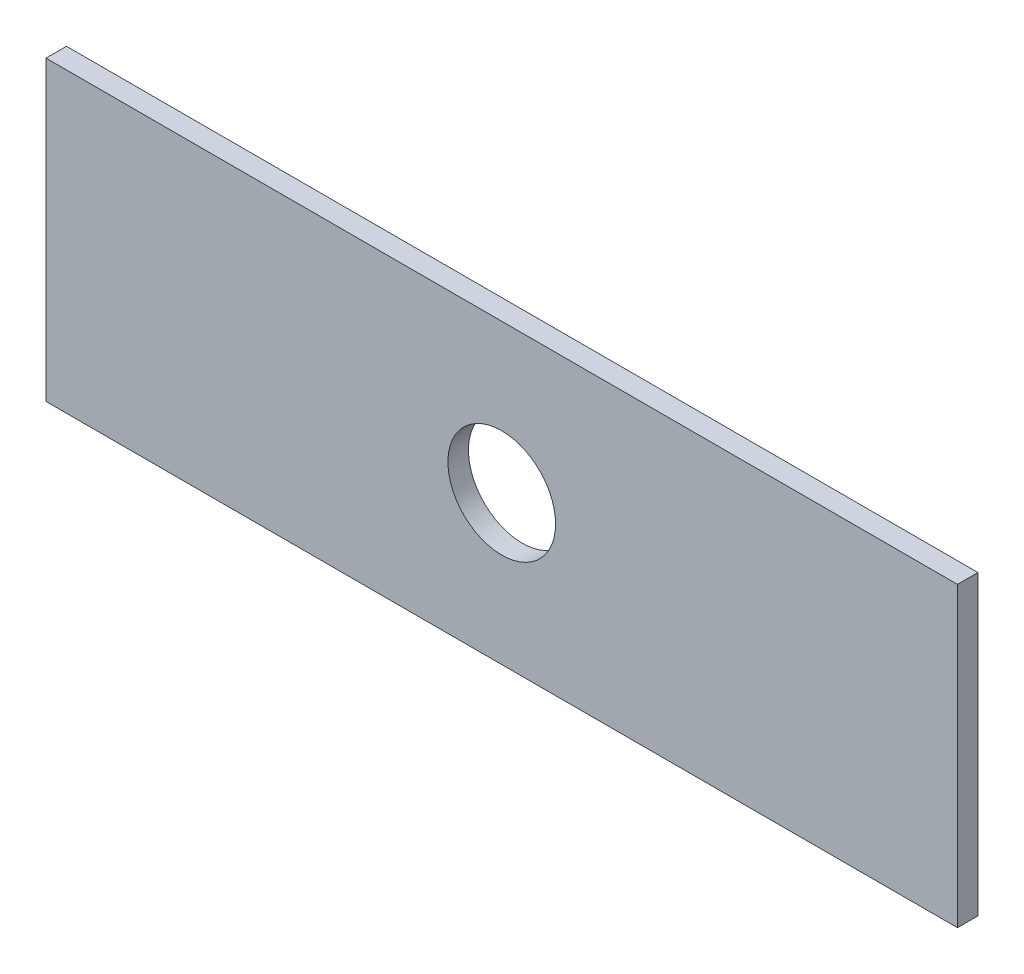
SolidWorks part; units mm, degrees
ref_plane "Front Plane" through (0, 0, 0) normal (0, 0, 1) x (1, 0, 0)
ref_plane "Top Plane" through (0, 0, 0) normal (0, 1, 0) x (1, 0, 0)
ref_plane "Right Plane" through (0, 0, 0) normal (1, 0, 0) x (0, 0, -1)
sketch "Sketch2" plane through (0, 0, 0) normal (0, 0, 1) x (1, 0, 0)
  line L0 (-83.6741, 29.186) -> (94.1259, 29.186)
  line L1 (-83.6741, 29.186) -> (-83.6741, -28.814)
  line L2 (-83.6741, -28.814) -> (94.1259, -28.814)
  line L3 (94.1259, 29.186) -> (94.1259, -28.814)
  dimension "D1" = 177.8
  dimension "D2" = 58
extrude "Boss-Extrude2" add sketch "Sketch2" along normal blind 4
sketch "Sketch3" plane through (0, 0, 4) normal (0, 0, 1) x (1, 0, 0)
  line L0 (5.2259, 29.186) -> (5.2259, -28.814) construction
  line L1 (94.1259, 29.186) -> (-83.6741, 29.186) construction
  line L2 (-83.6741, -28.814) -> (94.1259, -28.814) construction
  line L3 (-83.6741, 0.186) -> (94.1259, 0.186) construction
  line L4 (-83.6741, 29.186) -> (-83.6741, -28.814) construction
  line L5 (94.1259, -28.814) -> (94.1259, 29.186) construction
  circle A0 centre (5.2259, 0.186) radius 10.5
  dimension "D1" = 21
extrude "Cut-Extrude1" cut sketch "Sketch3" against normal up to next
